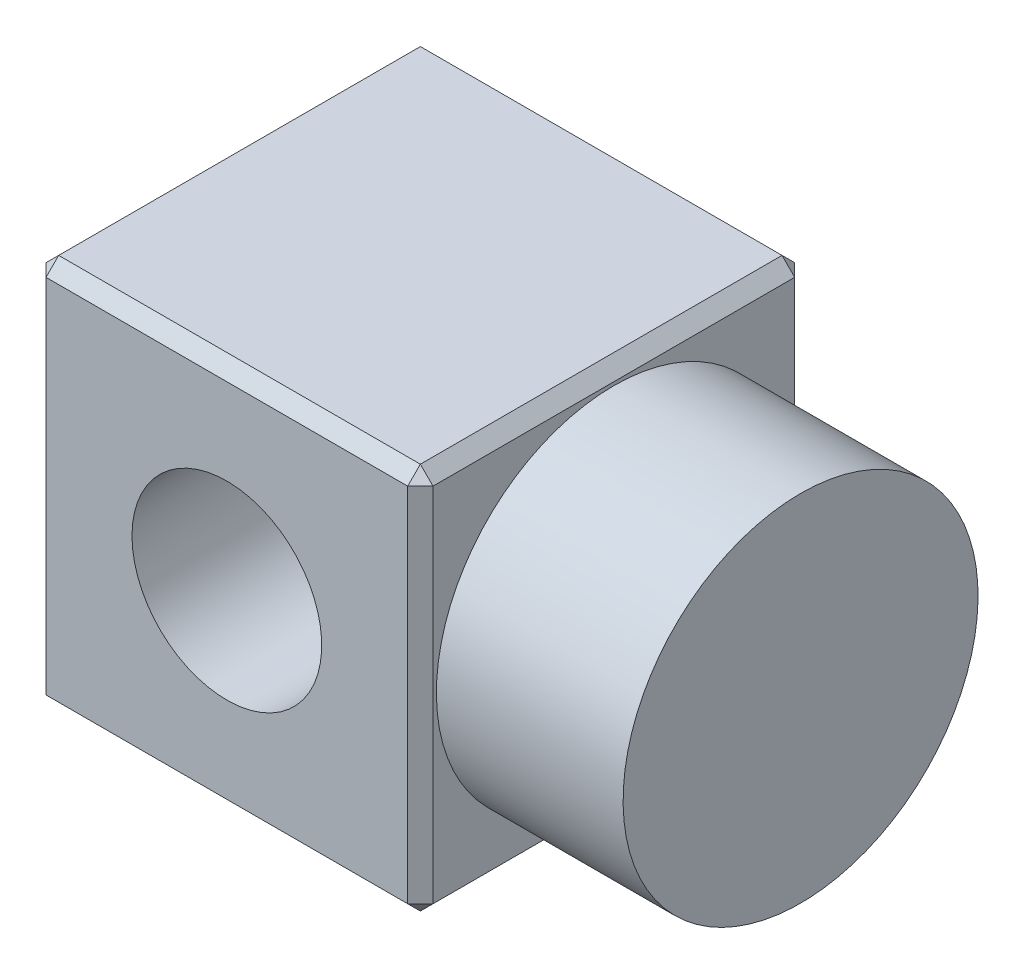
SolidWorks part; units mm, degrees
ref_plane "Front Plane" through (0, 0, 0) normal (0, 0, 1) x (1, 0, 0)
ref_plane "Top Plane" through (0, 0, 0) normal (0, 1, 0) x (1, 0, 0)
ref_plane "Right Plane" through (0, 0, 0) normal (1, 0, 0) x (0, 0, -1)
sketch "Sketch1" plane through (1848.7405, 0, 0) normal (-1, 0, 0) x (0, 0, 1)
  line L1 (-38.165, -38.165) -> (38.165, -38.165)
  line L2 (-38.165, -38.165) -> (-38.165, 38.165)
  line L3 (-38.165, 38.165) -> (38.165, 38.165)
  line L4 (38.165, -38.165) -> (38.165, 38.165)
  line L5 (-38.165, -38.165) -> (38.165, 38.165) construction
  line L6 (-38.165, 38.165) -> (38.165, -38.165) construction
  circle A0 centre (0, 0) radius 35 construction
  dimension "D1" = 70
  dimension "D2" = 76.33
  dimension "D3" = 76.33
extrude "Boss-Extrude1" add sketch "Sketch1" along normal blind 76.33 contours A0 | L2 L1 L4 L3
sketch "Sketch2" plane through (1848.7405, 0, 0) normal (1, 0, 0) x (0, 0, -1)
  circle A0 centre (0, 0) radius 35
  dimension "D1" = 70
extrude "Boss-Extrude2" add sketch "Sketch2" along normal blind 36.82
chamfer "Chamfer1" distance 2.5 angle 45 12 edges at (1848.7405, 0, -38.165) (1810.5755, 38.165, -38.165) (1848.7405, 38.165, 0) (1810.5755, 38.165, 38.165) (1848.7405, 0, 38.165) (1810.5755, -38.165, -38.165) (1848.7405, -38.165, 0) (1810.5755, -38.165, 38.165) (1772.4105, 0, 38.165) (1772.4105, -38.165, 0) (1772.4105, 0, -38.165) (1772.4105, 38.165, 0)
sketch "Sketch3" plane through (0, 0, -38.165) normal (0, 0, -1) x (-1, 0, 0)
  line L0 (-1810.5755, 35.665) -> (-1810.5755, -35.665) construction
  line L4 (-1774.9105, 35.665) -> (-1846.2405, 35.665)
  line L5 (-1846.2405, 35.665) -> (-1846.2405, -35.665)
  line L6 (-1846.2405, -35.665) -> (-1774.9105, -35.665)
  line L7 (-1774.9105, -35.665) -> (-1774.9105, 35.665)
  line L8 (-1774.9105, 35.665) -> (-1846.2405, 35.665)
  line L9 (-1846.2405, 35.665) -> (-1846.2405, -35.665)
  line L10 (-1846.2405, -35.665) -> (-1774.9105, -35.665)
  line L11 (-1774.9105, -35.665) -> (-1774.9105, 35.665)
  circle A0 centre (-1810.5755, 0) radius 18.71
  dimension "D2" = 37.42
  dimension "D1" = 0
extrude "Cut-Extrude1" cut sketch "Sketch3" against normal up to next contours A0 L0 | L0 A0
